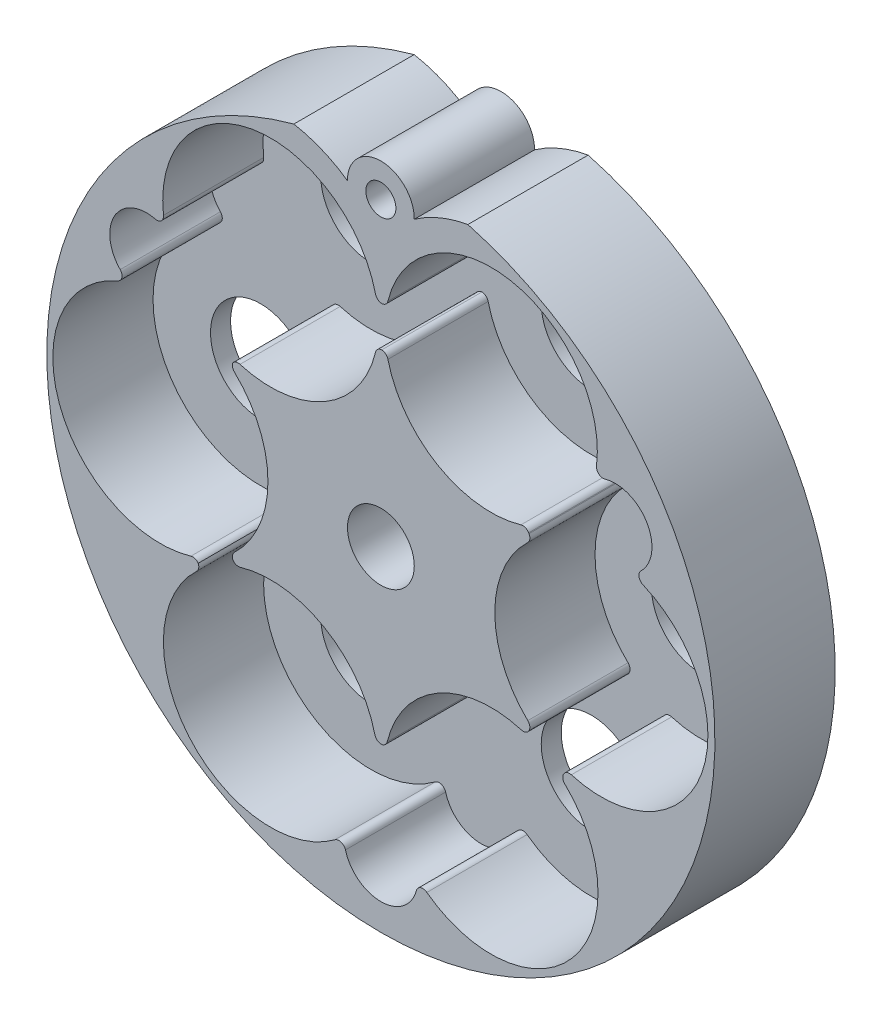
SolidWorks part; units mm, degrees
ref_plane "前视基准面" through (0, 0, 0) normal (0, 0, 1) x (1, 0, 0)
ref_plane "上视基准面" through (0, 0, 0) normal (0, 1, 0) x (1, 0, 0)
ref_plane "右视基准面" through (0, 0, 0) normal (1, 0, 0) x (0, 0, -1)
ref_plane "基准面4" through (0, 0, 0) normal (0, 0, -1) x (-1, 0, 0)
sketch "草图1" plane through (0, 0, 0) normal (0, 0, -1) x (-1, 0, 0)
  arc A0 (-63.0229, -268.3257) -> (-36.9771, -268.3257) centre (-50, -316.6) ccw
  arc A1 (-36.9771, -268.3257) -> (-45.0003, -271.6583) centre (-33.5, -288.0212) ccw
  arc A2 (-45.0003, -271.6583) -> (-54.9997, -271.6583) centre (-50, -271.6) ccw
  arc A3 (-54.9997, -271.6583) -> (-63.0229, -268.3257) centre (-66.5, -288.0212) ccw
extrude "凸台-拉伸1" add sketch "草图1" against normal blind 18
sketch "草图2" plane through (0, 0, 18) normal (0, 0, 1) x (1, 0, 0)
  line L0 (76.9562, -333.0682) -> (77.7654, -331.6666)
  arc A0 (55.3163, -358.5097) -> (56.8839, -357.9667) centre (56.2829, -358.766) cw
  arc A1 (56.8839, -357.9667) -> (76.9562, -333.0682) centre (66.5, -345.1788) ccw
  arc A2 (77.7654, -331.6666) -> (89.2292, -301.9167) centre (83, -316.6) ccw
  arc A3 (89.2292, -301.9167) -> (88.9204, -300.2813) centre (89.6198, -300.9961) cw
  arc A4 (88.9204, -300.2813) -> (83.5484, -291.0658) centre (85.074, -296.35) ccw
  arc A5 (83.5484, -291.0658) -> (82.2787, -289.9818) centre (83.271, -290.1051) cw
  arc A6 (82.2787, -289.9818) -> (51.0518, -284.2578) centre (66.5, -288.0212) ccw
  arc A7 (51.0518, -284.2578) -> (50.1286, -285.02) centre (50.0802, -284.0212) cw
  arc A8 (50.1286, -285.02) -> (49.2046, -284.2544) centre (50.177, -284.0212) cw
  arc A9 (49.2046, -284.2544) -> (17.4618, -289.9183) centre (33.5, -288.0212) ccw
  arc A10 (17.4618, -289.9183) -> (16.2314, -291.0072) centre (16.4687, -290.0357) cw
  arc A11 (16.2314, -291.0072) -> (10.9831, -300.1845) centre (14.926, -296.35) ccw
  arc A12 (10.9831, -300.1845) -> (10.66, -301.8009) centre (10.2662, -300.8817) cw
  arc A13 (10.66, -301.8009) -> (21.5651, -332.0392) centre (17, -316.6) ccw
  arc A14 (21.5651, -332.0392) -> (22.6605, -332.4142) centre (21.8487, -332.9982) cw
  arc A15 (22.6605, -332.4142) -> (22.438, -333.5498) centre (21.7488, -332.8252) cw
  arc A16 (22.438, -333.5498) -> (43.1311, -358.018) centre (33.5, -345.1788) ccw
  arc A17 (43.1311, -358.018) -> (44.6956, -358.5537) centre (43.7311, -358.818) cw
  arc A18 (44.6956, -358.5537) -> (55.3163, -358.5097) centre (50, -357.1) ccw
extrude "切除-拉伸1" cut sketch "草图2" against normal blind 15
sketch "草图3" plane through (0, 0, 3) normal (0, 0, 1) x (1, 0, 0)
  line L0 (71.7091, -303.0436) -> (72.5693, -304.5334)
  line L1 (72.5693, -328.6666) -> (71.76, -330.0682)
  arc A0 (50.9492, -341.4141) -> (50.0257, -342.1777) centre (49.9773, -341.1788) cw
  arc A1 (50.0257, -342.1777) -> (49.1021, -341.4134) centre (50.0742, -341.1788) cw
  arc A2 (49.1021, -341.4134) -> (28.9599, -329.7844) centre (33.5, -345.1788) ccw
  arc A3 (28.9599, -329.7844) -> (27.8653, -329.4092) centre (28.677, -328.8252) cw
  arc A4 (27.8653, -329.4092) -> (28.0882, -328.2731) centre (28.7769, -328.9982) cw
  arc A5 (28.0882, -328.2731) -> (28.0882, -304.9269) centre (17, -316.6) ccw
  arc A6 (28.0882, -304.9269) -> (27.8452, -303.8386) centre (28.7769, -304.2018) cw
  arc A7 (27.8452, -303.8386) -> (28.9098, -303.5051) centre (28.6256, -304.4639) cw
  arc A8 (28.9098, -303.5051) -> (49.2046, -291.7879) centre (33.5, -288.0212) ccw
  arc A9 (49.2046, -291.7879) -> (50.1286, -291.0223) centre (50.177, -292.0212) cw
  arc A10 (50.1286, -291.0223) -> (51.0518, -291.7845) centre (50.0802, -292.0212) cw
  arc A11 (51.0518, -291.7845) -> (71.7091, -303.0436) centre (66.5, -288.0212) ccw
  arc A12 (72.5693, -304.5334) -> (72.5693, -328.6666) centre (83, -316.6) ccw
  arc A13 (71.76, -330.0682) -> (50.9492, -341.4141) centre (66.5, -345.1788) ccw
extrude "凸台-拉伸2" add sketch "草图3" along normal blind 15
hole_wizard "Ø4.5 (4.5) 直径孔1" positions "草图5" profile "草图4" hole size "Ø4.5" standard "ANSI Metric"
sketch "草图5" plane through (0, 0, 18) normal (0, 0, 1) x (1, 0, 0)
  point P0 (50, -271.6)
sketch "草图4" plane through (50, -271.6, 18) normal (1, 0, 0) x (0, -1, 0)
  line L0 (0, 0) -> (0, 18)
  line L1 (0, 18) -> (2.25, 18)
  line L2 (2.25, 18) -> (2.25, 0)
  line L5 (2.25, 0) -> (0, 0)
  line L11 (0, -6.35) -> (0, 107.95) construction
  dimension "通孔孔直径" = 4.5
  dimension "通孔孔深度" = 18
hole_wizard "Ø10.0 (10) 直径孔1" positions "草图7" profile "草图6" hole size "Ø10.0" standard "ANSI Metric"
sketch "草图7" plane through (0, 0, 18) normal (0, 0, 1) x (1, 0, 0)
  point P0 (50, -316.6)
sketch "草图6" plane through (50, -316.6, 18) normal (1, 0, 0) x (0, -1, 0)
  line L0 (0, 0) -> (0, 18)
  line L1 (0, 18) -> (5, 18)
  line L2 (5, 18) -> (5, 0)
  line L5 (5, 0) -> (0, 0)
  line L11 (0, -6.35) -> (0, 107.95) construction
  dimension "通孔孔直径" = 10
  dimension "通孔孔深度" = 18
hole_wizard "Ø15.0 (15) 直径孔1" positions "草图9" profile "草图8" hole size "Ø15.0" standard "ANSI Metric"
sketch "草图9" plane through (0, 0, 0) normal (0, 0, -1) x (-1, 0, 0)
  point P0 (-33.5, -288.0212)
  point P1 (-83, -316.6)
  point P2 (-66.5, -345.1788)
  point P3 (-33.5, -345.1788)
  point P4 (-66.5, -288.0212)
  point P5 (-17, -316.6)
sketch "草图8" plane through (33.5, -288.0212, 0) normal (1, 0, 0) x (0, 1, 0)
  line L0 (0, 0) -> (0, 18)
  line L1 (0, 18) -> (7.5, 18)
  line L2 (7.5, 18) -> (7.5, 0)
  line L5 (7.5, 0) -> (0, 0)
  line L11 (0, -6.35) -> (0, 107.95) construction
  dimension "通孔孔直径" = 15
  dimension "通孔孔深度" = 18
fillet "圆角1" radius 1 6 edges at (72.5693, -328.6666, 10.5) (72.5693, -304.5334, 10.5) (76.9562, -333.0682, 10.5) (71.7091, -303.0436, 10.5) (77.7654, -331.6666, 10.5) (71.76, -330.0682, 10.5)
